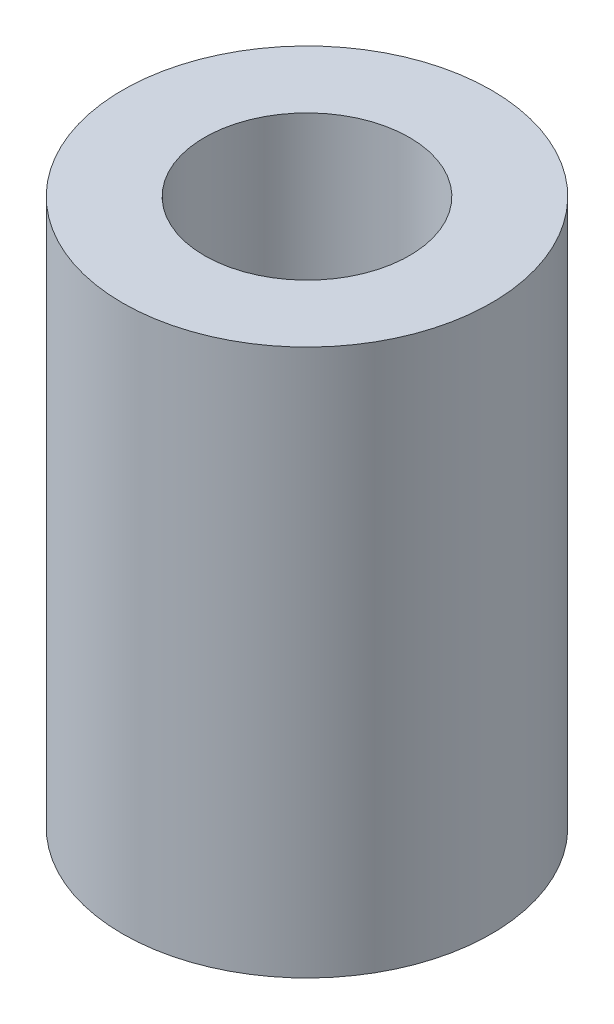
SolidWorks part; units mm, degrees
ref_plane "Plano frontal" through (0, 0, 0) normal (0, 0, 1) x (1, 0, 0)
ref_plane "Plano superior" through (0, 0, 0) normal (0, 1, 0) x (1, 0, 0)
ref_plane "Plano direito" through (0, 0, 0) normal (1, 0, 0) x (0, 0, -1)
sketch "Esboço1" plane through (0, 0, 0) normal (0, 1, 0) x (1, 0, 0)
  circle A0 centre (0, 0) radius 1.875
  circle A2 centre (0, 0) radius 3.375
  dimension "D1" = 3.75
  dimension "D2" = 1.5
extrude "Ressalto-extrusão1" add sketch "Esboço1" along normal blind 10
